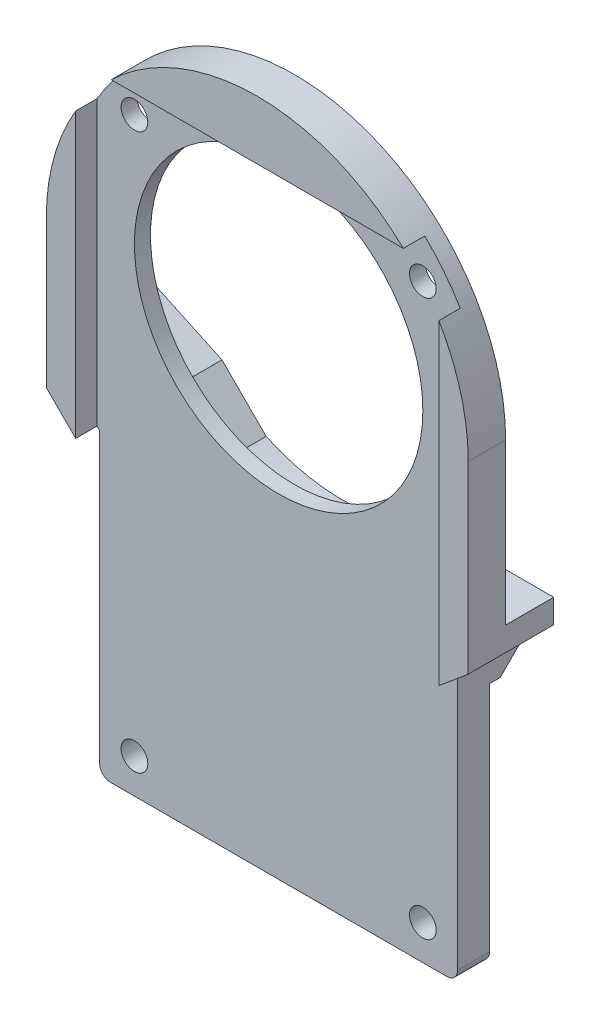
SolidWorks part; units mm, degrees
material "ABS"
ref_plane "前视基准面" through (0, 0, 0) normal (0, 0, 1) x (1, 0, 0)
ref_plane "上视基准面" through (0, 0, 0) normal (0, 1, 0) x (1, 0, 0)
ref_plane "右视基准面" through (0, 0, 0) normal (1, 0, 0) x (0, 0, -1)
other "Configuration Table"
sketch "草图1" plane through (0, 0, 0) normal (0, 0, 1) x (1, 0, 0)
  line L0 (-16.75, 13.75) -> (-16.75, -44.75) construction
  line L1 (-16.75, -44.75) -> (16.75, -44.75)
  line L2 (16.75, -44.75) -> (16.75, 13.75) construction
  line L3 (16.75, 13.75) -> (-16.75, 13.75) construction
  line L4 (0, 13.75) -> (0, -44.75) construction
  line L5 (-13.5, -41.5) -> (13.5, -41.5) construction
  line L6 (13.5, -41.5) -> (13.5, 10.5) construction
  line L7 (13.5, 10.5) -> (-13.5, 10.5) construction
  line L8 (-13.5, 10.5) -> (-13.5, -41.5) construction
  line L9 (-16.75, -16.75) -> (-19.75, -13.75)
  line L10 (-19.75, -13.75) -> (-19.75, 0)
  line L11 (-16.75, -16.75) -> (-16.75, -44.75)
  line L12 (16.75, -19.75) -> (19.75, -17.2327)
  line L13 (19.75, -17.2327) -> (19.75, 0)
  line L14 (16.75, -19.75) -> (16.75, -44.75)
  line L15 (19.75, 0) -> (-19.75, 0) construction
  circle A0 centre (0, 0) radius 13.5
  circle A2 centre (-13.5, -41.5) radius 1.25
  circle A3 centre (13.5, -41.5) radius 1.25
  circle A4 centre (-13.5, 10.5) radius 1.25
  circle A5 centre (13.5, 10.5) radius 1.25
  arc A9 (19.75, 0) -> (-19.75, 0) centre (0, 0) ccw
  dimension "D4" = 27
  dimension "D5" = 45
  dimension "D7" = 10.5
  dimension "D9" = 2.5
  dimension "D11" = 33.5
  dimension "D17" = 2.5
  dimension "D1" = 13.75
  dimension "D3" = 58.5
  dimension "D6" = 52
  dimension "D8" = 27
  dimension "D10" = 3
  dimension "D12" = 28
  dimension "D13" = 3
  dimension "D14" = 50
  dimension "D15" = 25
extrude "凸台-拉伸1" add sketch "草图1" along normal blind 5 contours L10 L9 L11 L1 L2
sketch "草图2" plane through (0, 0, 0) normal (0, 0, -1) x (-1, 0, 0)
  circle A0 centre (-13.5, 10.5) radius 2.75 construction
  circle A1 centre (13.5, 10.5) radius 2.75 construction
  circle A2 centre (-13.5, -41.5) radius 2.75
  circle A3 centre (13.5, -41.5) radius 2.75
  circle A6 centre (-13.5, 10.5) radius 1.25 construction
  circle A7 centre (13.5, 10.5) radius 1.25 construction
  circle A8 centre (-13.5, -41.5) radius 1.25 construction
  circle A9 centre (13.5, -41.5) radius 1.25 construction
  dimension "D1" = 5.5
extrude "切除-拉伸1" cut sketch "草图2" against normal blind 1
sketch "草图4" plane through (0, 0, 5) normal (0, 0, 1) x (1, 0, 0)
  line L1 (17, -44.75) -> (-17, -44.75)
  line L2 (17, -44.75) -> (17, 14.25)
  line L3 (17, 14.25) -> (-17, 14.25)
  line L4 (-17, -44.75) -> (-17, 14.25)
  line L5 (17, -44.75) -> (-17, 14.25) construction
  line L6 (17, 14.25) -> (-17, -44.75) construction
  line L7 (0, -44.75) -> (0, 0) construction
  line L8 (-16.75, -44.75) -> (16.75, -44.75) construction
  point P4 (0, -15.25)
  dimension "D1" = 34
  dimension "D2" = 59
extrude "切除-拉伸3" cut sketch "草图4" against normal blind 2
sketch "草图5" plane through (0, 0, 0) normal (0, 0, -1) x (-1, 0, 0)
  line L0 (0, 0) -> (0, 18.0064) construction
  line L1 (16.75, -16.75) -> (16.75, -44.75) construction
  line L2 (-16.75, -22) -> (13.75, -22)
  line L3 (-16.75, -44.75) -> (-16.75, -19.75) construction
  line L4 (-16.75, -22) -> (-16.75, -19.75)
  line L5 (-16.75, -19.75) -> (-19.75, -17.2327)
  line L6 (16.75, -19) -> (13.75, -22)
  line L8 (6.3393, -13.5946) -> (19.75, -7.3411) construction
  line L11 (11.3008, -11.281) -> (19.75, -7.3411)
  line L12 (19.75, 0) -> (19.75, -13.75) construction
  line L13 (16.75, -19) -> (16.75, -16.75)
  line L14 (19.75, -13.75) -> (16.75, -16.75) construction
  line L15 (16.75, -16.75) -> (19.75, -13.75)
  line L16 (19.75, -13.75) -> (19.75, -7.3411)
  line L17 (0, 0) -> (0, -22) construction
  line L19 (11.3008, -11.281) -> (7.1659, -15.4159)
  line L20 (7.1659, -15.4159) -> (13.75, -22) construction
  line L21 (-19.75, -15) -> (-8, -15)
  line L22 (-16.75, -19.75) -> (-19.75, -17.2327) construction
  line L23 (-19.75, -17.2327) -> (-19.75, -15)
  line L24 (-19.75, -17.2327) -> (-19.75, 0) construction
  circle A3 centre (0, 0) radius 15 construction
  arc A6 (-8, -15) -> (7.1659, -15.4159) centre (0, 0) ccw
  dimension "D1" = 30
  dimension "D2" = 2
  dimension "D3" = 25
  dimension "D4" = 45
  dimension "D5" = 3
  dimension "D7" = 5
  dimension "D6" = 3
  dimension "D8" = 90
extrude "凸台-拉伸2" add sketch "草图5" along normal blind 3
chamfer "倒角1" distance 2 angle 45 4 edges at (-15.25, -20.5, -3) (1.5, -22, -3) (-16.75, -17.875, -3) (-18.25, -15.25, -3)
sketch "草图8" plane through (0, 0, 0) normal (0, 0, -1) x (-1, 0, 0)
  line L5 (-19.75, -15) -> (-8, -15)
  line L6 (7.1659, -15.4159) -> (11.3008, -11.281)
  line L7 (11.3008, -11.281) -> (19.75, -7.3411)
  line L8 (19.75, -7.3411) -> (19.75, 0)
  line L9 (-19.75, 0) -> (-19.75, -15)
  line L10 (-19.75, -15) -> (-8, -15)
  line L12 (11.3008, -11.281) -> (19.75, -7.3411)
  line L13 (19.75, -7.3411) -> (19.75, 0)
  line L14 (-19.75, 0) -> (-19.75, -15)
  line L15 (7.1659, -15.4159) -> (11.3008, -11.281)
  arc A2 (-8, -15) -> (7.1659, -15.4159) centre (0, 0) ccw
  arc A3 (19.75, 0) -> (-19.75, 0) centre (0, 0) ccw
  arc A5 (19.75, 0) -> (-19.75, 0) centre (0, 0) ccw
  arc A8 (-8, -15) -> (7.1659, -15.4159) centre (0, 0) ccw
  dimension "D1" = 0
extrude "切除-拉伸4" cut sketch "草图8" against normal offset from surface (1.5 mm away) 1.5 up to face at (-12.25, -41.5, 3)
fillet "圆角3" radius 1 2 edges at (16.75, -44.75, 1.5) (-16.75, -44.75, 1.5)
